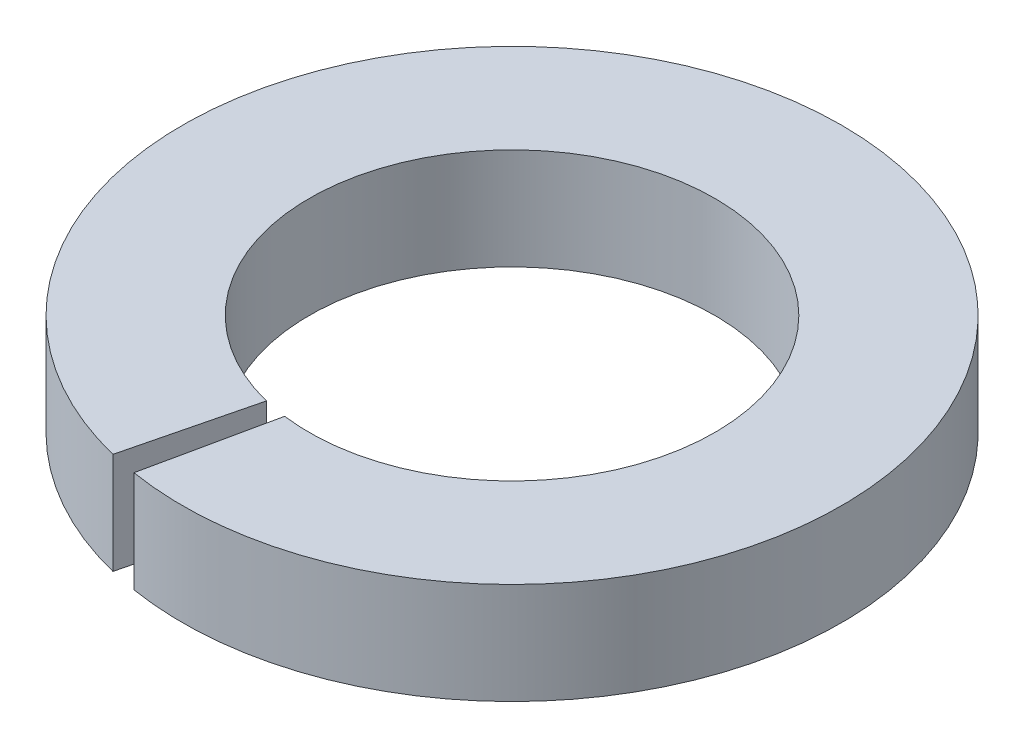
SolidWorks part; units mm, degrees
ref_plane "Спереди" through (0, 0, 0) normal (0, 0, 1) x (1, 0, 0)
ref_plane "Сверху" through (0, 0, 0) normal (0, 1, 0) x (1, 0, 0)
ref_plane "Справа" through (0, 0, 0) normal (1, 0, 0) x (0, 0, -1)
sketch "Эскиз1" plane through (0, 0, 0) normal (0, 1, 0) x (1, 0, 0)
  line L0 (-0.481, -1.9413) -> (-0.7816, -3.1546)
  line L1 (-0.5211, -3.208) -> (-0.2598, -1.9831)
  arc A0 (-0.2598, -1.9831) -> (-0.481, -1.9413) centre (0, 0) ccw
  arc A1 (-0.5211, -3.208) -> (-0.7816, -3.1546) centre (0, 0) ccw
  dimension "D1" = 6.5
  dimension "D2" = 4
extrude "Бобышка-Вытянуть1" add sketch "Эскиз1" along normal blind 1
